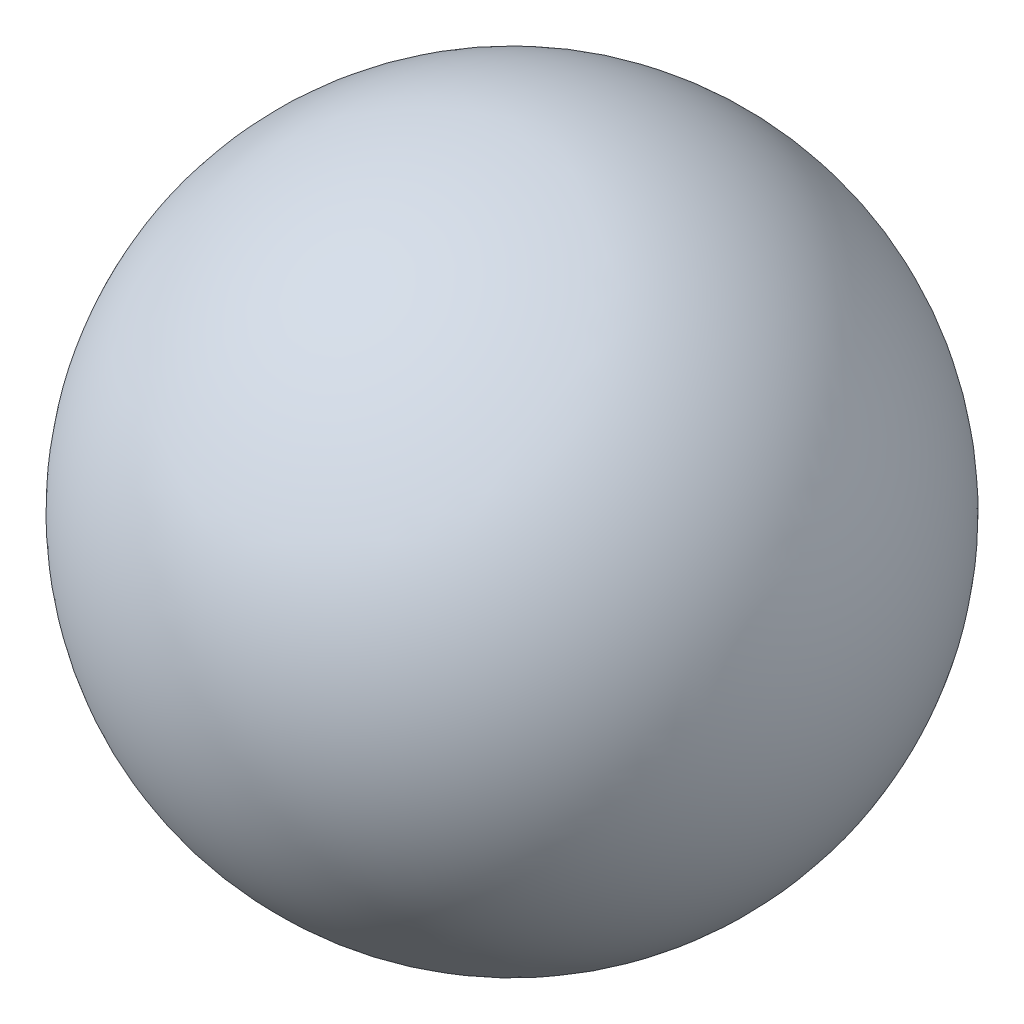
SolidWorks part; units mm, degrees
material "AISI 316 Paslanmaz Çelik Levha (SS)"
ref_plane "Ön Düzlem" through (0, 0, 0) normal (0, 0, 1) x (1, 0, 0)
ref_plane "Üst Düzlem" through (0, 0, 0) normal (0, 1, 0) x (1, 0, 0)
ref_plane "Sağ Düzlem" through (0, 0, 0) normal (1, 0, 0) x (0, 0, -1)
sketch "Çizim1" plane through (0, 0, 0) normal (0, 1, 0) x (1, 0, 0)
  line L0 (-7.5, 0) -> (7.5, 0)
  circle A0 centre (0, 0) radius 7.5
  dimension "D1" = 15
ref_axis "Eksen1" through (-8.25, 0, 0) along (1, 0, 0)
revolve "Döndür3" add sketch "Çizim1" angle 360 about axis through (-8.25, 0, 0) along (1, 0, 0)
